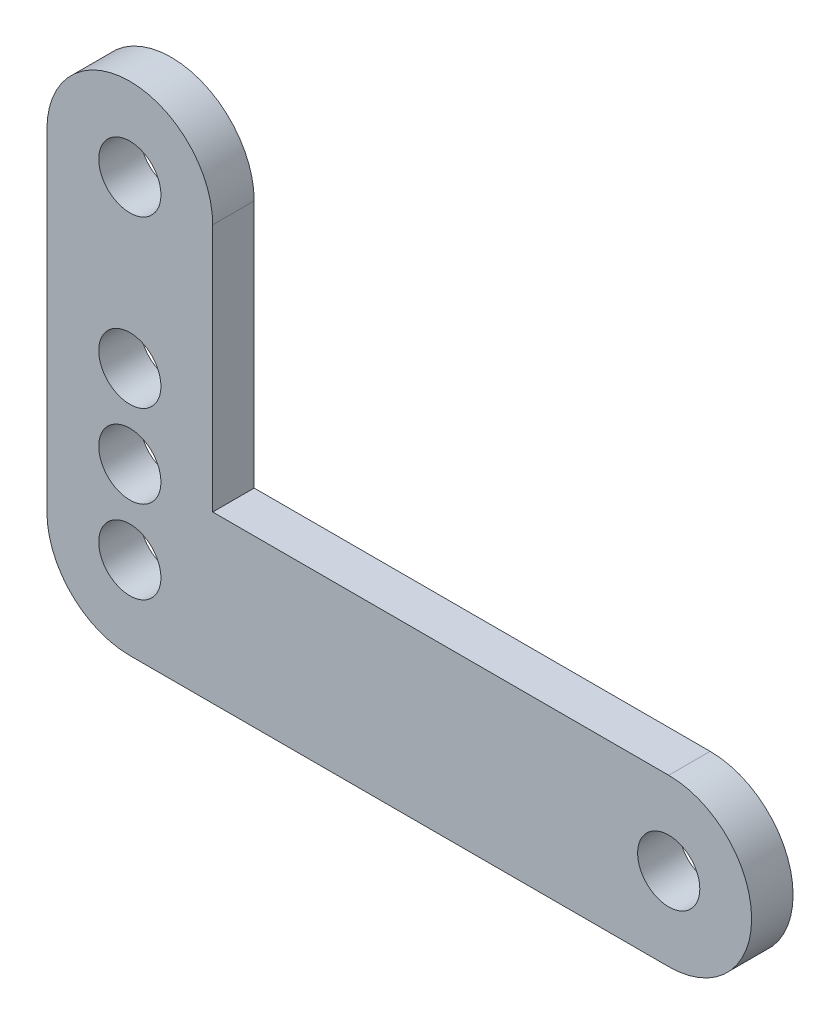
SolidWorks part; units mm, degrees
ref_plane "Front Plane" through (0, 0, 0) normal (0, 0, 1) x (1, 0, 0)
ref_plane "Top Plane" through (0, 0, 0) normal (0, 1, 0) x (1, 0, 0)
ref_plane "Right Plane" through (0, 0, 0) normal (1, 0, 0) x (0, 0, -1)
sketch "Sketch1" plane through (0, 0, 0) normal (0, 0, 1) x (1, 0, 0)
  line L0 (0, 0) -> (-82.55, 0) construction
  line L1 (0, -12.7) -> (-82.55, -12.7)
  line L2 (0, 12.7) -> (-82.55, 12.7)
  line L3 (-82.55, 0) -> (-82.55, 50.8) construction
  line L4 (-95.25, 0) -> (-95.25, 50.8)
  line L5 (-69.85, 0) -> (-69.85, 50.8)
  arc A0 (0, -12.7) -> (0, 12.7) centre (0, 0) ccw
  arc A1 (-82.55, 12.7) -> (-82.55, -12.7) centre (-82.55, 0) ccw
  arc A2 (-95.25, 0) -> (-69.85, 0) centre (-82.55, 0) ccw
  arc A3 (-69.85, 50.8) -> (-95.25, 50.8) centre (-82.55, 50.8) ccw
  circle A4 centre (0, 0) radius 4.7625
  circle A5 centre (-82.55, 0) radius 4.7625
  circle A6 centre (-82.55, 50.8) radius 4.7625
  circle A7 centre (-82.55, 12.7) radius 4.7625
  circle A8 centre (-82.55, 25.4) radius 4.7625
  point P3 (-41.275, 0)
  point P8 (-82.55, 25.4)
  dimension "D4" = 9.525
  dimension "D5" = 9.525
  dimension "D6" = 9.525
  dimension "D1" = 82.55
  dimension "D2" = 50.8
  dimension "D3" = 25.4
extrude "Boss-Extrude1" add sketch "Sketch1" along normal blind 6.35 contours L5 A3 L4 A1 L2 A6 | A1 A2 L5 L2 A5 | A2 L1 A0 L2 L5 A4
